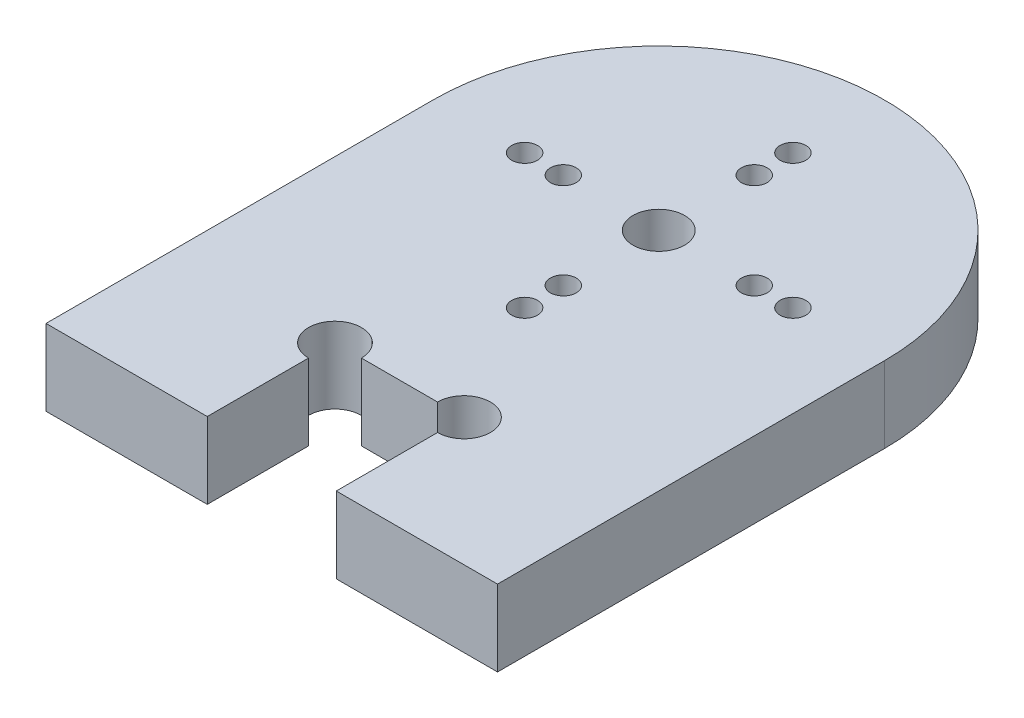
SolidWorks part; units mm, degrees
ref_plane "Front Plane" through (0, 0, 0) normal (0, 0, 1) x (1, 0, 0)
ref_plane "Top Plane" through (0, 0, 0) normal (0, 1, 0) x (1, 0, 0)
ref_plane "Right Plane" through (0, 0, 0) normal (1, 0, 0) x (0, 0, -1)
sketch "Sketch1" plane through (0, 0, 0) normal (0, 1, 0) x (1, 0, 0)
  line L1 (-17.5, 12.5) -> (17.5, 12.5)
  line L2 (-17.5, 12.5) -> (-17.5, -12.5)
  line L3 (-17.5, -12.5) -> (17.5, -12.5)
  line L4 (17.5, 12.5) -> (17.5, -12.5)
  line L5 (-17.5, 12.5) -> (17.5, -12.5) construction
  line L6 (-17.5, -12.5) -> (17.5, 12.5) construction
  circle A0 centre (0, 12.5) radius 17.5
  circle A1 centre (0, 22.9) radius 1
  circle A2 centre (0, 19.9) radius 1
  circle A3 centre (0, 12.5) radius 2
  circle A4 centre (7.4, 12.5) radius 1
  circle A5 centre (10.4, 12.5) radius 1
  circle A6 centre (0, 5.1) radius 1
  circle A7 centre (0, 2.1) radius 1
  circle A8 centre (-7.4, 12.5) radius 1
  circle A9 centre (-10.4, 12.5) radius 1
  point P0 (0, 0)
  point P28 (0, 12.5)
  dimension "D3" = 2
  dimension "D4" = 3
  dimension "D5" = 7.4
  dimension "D6" = 4
  dimension "D1" = 25
  dimension "D2" = 35
  dimension "D7" = 4
extrude "Boss-Extrude1" add sketch "Sketch1" along normal blind 5.9 contours A9 L1 A8 A3 A4 A5 A0 A2 A1 | A9 L1 A0 A5 A4 A3 A8 A7 A6 | A0 L2 L3 L4
sketch "Sketch2" plane through (0, 5.9, 0) normal (0, 1, 0) x (1, 0, 0)
  line L1 (-5, -19.4) -> (5, -19.4)
  line L2 (-5, -19.4) -> (-5, -7.6)
  line L3 (-5, -7.6) -> (5, -7.6)
  line L4 (5, -19.4) -> (5, -7.6)
  line L5 (-5, -19.4) -> (5, -7.6) construction
  line L6 (-5, -7.6) -> (5, -19.4) construction
  point P0 (0, -13.5)
  dimension "D1" = 11.8
  dimension "D2" = 10
  dimension "D3" = 13.5
extrude "Cut-Extrude1" cut sketch "Sketch2" against normal blind 10
sketch "Sketch3" plane through (0, 0, 12.5) normal (0, 0, 1) x (1, 0, 0)
  line L4 (-17.5, 0) -> (-5, 0)
  line L5 (-5, 0) -> (-5, 5.9)
  line L6 (-5, 5.9) -> (-17.5, 5.9)
  line L7 (-17.5, 5.9) -> (-17.5, 0)
  line L8 (-17.5, 0) -> (-5, 0)
  line L9 (-5, 0) -> (-5, 5.9)
  line L10 (-5, 5.9) -> (-17.5, 5.9)
  line L11 (-17.5, 5.9) -> (-17.5, 0)
  line L12 (17.5, 5.9) -> (5, 5.9)
  line L13 (5, 5.9) -> (5, 0)
  line L14 (5, 0) -> (17.5, 0)
  line L15 (17.5, 0) -> (17.5, 5.9)
  line L16 (17.5, 5.9) -> (5, 5.9)
  line L17 (5, 5.9) -> (5, 0)
  line L18 (5, 0) -> (17.5, 0)
  line L19 (17.5, 0) -> (17.5, 5.9)
  dimension "D1" = 0
  dimension "D2" = 0
extrude "Boss-Extrude2" add sketch "Sketch3" along normal blind 5
sketch "Sketch4" plane through (0, 5.9, 0) normal (0, 1, 0) x (1, 0, 0)
  circle A0 centre (-5, -7.6) radius 2.05
  circle A1 centre (5, -7.6) radius 2.05
  dimension "D1" = 4.1
extrude "Cut-Extrude2" cut sketch "Sketch4" against normal up to next
equation "\"e\" = 5.9"
equation "\"D1@Boss-Extrude1\"=\"e\""
equation "\"D1@Sketch2\"= 2 * \"e\""
